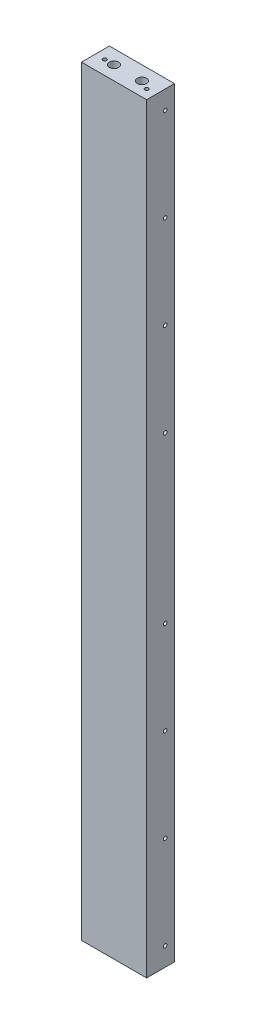
SolidWorks part; units mm, degrees
ref_plane "Front Plane" through (0, 0, 0) normal (0, 0, 1) x (1, 0, 0)
ref_plane "Top Plane" through (0, 0, 0) normal (0, 1, 0) x (1, 0, 0)
ref_plane "Right Plane" through (0, 0, 0) normal (1, 0, 0) x (0, 0, -1)
sketch "Sketch1" plane through (0, 0, 0) normal (0, 1, 0) x (1, 0, 0)
  line L1 (0, 0) -> (88.9, 0)
  line L2 (0, 0) -> (0, -38.1)
  line L3 (0, -38.1) -> (88.9, -38.1)
  line L4 (88.9, 0) -> (88.9, -38.1)
  dimension "D1" = 38.1
  dimension "D2" = 88.9
extrude "Boss-Extrude1" add sketch "Sketch1" along normal blind 1038.225
sketch "Sketch2" plane through (0, 1038.225, 0) normal (0, 1, 0) x (1, 0, 0)
  line L0 (0, 0) -> (0, -38.1) construction
  line L1 (25.4, -19.05) -> (63.5, -19.05) construction
  line L2 (88.9, 0) -> (0, 0) construction
  circle A0 centre (25.4, -19.05) radius 6.35
  circle A1 centre (63.5, -19.05) radius 6.35
  point P7 (0, -19.05)
  point P9 (44.45, 0)
  point P10 (44.45, -19.05)
  dimension "D1" = 12.7
  dimension "D2" = 12.7
  dimension "D3" = 38.1
extrude "Cut-Extrude1" cut sketch "Sketch2" against normal blind 19.05
sketch "Sketch3" plane through (0, 0, 0) normal (0, -1, 0) x (1, 0, 0)
  line L0 (25.4, 19.05) -> (63.5, 19.05) construction
  line L1 (0, 38.1) -> (88.9, 38.1) construction
  line L2 (0, 0) -> (0, 38.1) construction
  circle A0 centre (25.4, 19.05) radius 6.35
  circle A1 centre (63.5, 19.05) radius 6.35
  point P6 (44.45, 38.1)
  point P7 (44.45, 19.05)
  point P10 (0, 19.05)
  dimension "D1" = 12.7
  dimension "D2" = 12.7
  dimension "D3" = 38.1
extrude "Cut-Extrude2" cut sketch "Sketch3" against normal blind 19.05
sketch "Sketch4" plane through (0, 1038.225, 0) normal (0, 1, 0) x (1, 0, 0)
  line L0 (88.9, -38.1) -> (88.9, 0) construction
  line L1 (88.9, 0) -> (0, 0) construction
  point P0 (12.7, -19.05)
  point P1 (76.2, -25.4)
  dimension "D1" = 76.2
  dimension "D2" = 12.7
  dimension "D3" = 25.4
  dimension "D4" = 19.05
sketch "Sketch5" plane through (0, 0, 0) normal (0, -1, 0) x (1, 0, 0)
  line L0 (0, 0) -> (0, 38.1) construction
  line L1 (88.9, 0) -> (0, 0) construction
  point P0 (44.45, 25.4)
  dimension "D1" = 44.45
  dimension "D2" = 25.4
hole_wizard "#10 (0.1935) Diameter Hole1" positions "3DSketch1" profile "Sketch6" hole size "#10" standard "ANSI Inch"
sketch3d "3DSketch1"
  point P0 (44.45, 0, 25.4)
  point P3 (12.7, 1038.225, 19.05)
  point P6 (76.2, 1038.225, 25.4)
sketch "Sketch6" plane through (44.45, 0, 25.4) normal (1, 0, 0) x (0, 0, -1)
  line L0 (0, 0) -> (0, 77.6766)
  line L1 (0, 77.6766) -> (2.4574, 76.2)
  line L2 (2.4574, 76.2) -> (2.4574, 0)
  line L5 (2.4574, 0) -> (0, 0)
  line L10 (0, 77.6766) -> (-2.4575, 76.2) construction
  line L11 (0, -6.35) -> (0, 107.95) construction
  dimension "Hole Dia." = 4.9149
  dimension "Hole Depth" = 76.2
  dimension "Drill Angle" = 118
sketch "Sketch8" plane through (88.9, 0, 0) normal (1, 0, 0) x (0, 0, -1)
  line L0 (-12.7, 1038.225) -> (-12.7, 0) construction
  line L2 (-38.1, 1038.225) -> (0, 1038.225) construction
  line L3 (-38.1, 0) -> (0, 0) construction
  line L6 (0, 519.1125) -> (-38.1, 519.1125) construction
  line L7 (0, 1038.225) -> (0, 0) construction
  line L8 (-38.1, 1038.225) -> (-38.1, 0) construction
  point P3 (-12.7, 1012.825)
  point P4 (-12.7, 885.825)
  point P5 (-12.7, 25.4)
  point P6 (-12.7, 152.4)
  point P7 (-12.7, 279.4)
  point P8 (-12.7, 406.4)
  point P9 (-12.7, 758.825)
  point P10 (-12.7, 631.825)
  dimension "D1" = 25.4
  dimension "D2" = 127
  dimension "D3" = 127
  dimension "D4" = 127
  dimension "D5" = 12.7
  dimension "D6" = 12.7
hole_wizard "#10 (0.1935) Diameter Hole2" positions "3DSketch3" profile "Sketch12" hole size "#10" standard "ANSI Inch"
sketch3d "3DSketch3"
  point P0 (88.9, 25.4, 12.7)
  point P3 (88.9, 152.4, 12.7)
  point P6 (88.9, 279.4, 12.7)
  point P9 (88.9, 406.4, 12.7)
  point P12 (88.9, 631.825, 12.7)
  point P15 (88.9, 758.825, 12.7)
  point P18 (88.9, 885.825, 12.7)
  point P21 (88.9, 1012.825, 12.7)
sketch "Sketch12" plane through (88.9, 25.4, 12.7) normal (0, 1, 0) x (0, 0, -1)
  line L0 (0, 0) -> (0, 52.2766)
  line L1 (0, 52.2766) -> (2.4574, 50.8)
  line L2 (2.4574, 50.8) -> (2.4574, 0)
  line L5 (2.4574, 0) -> (0, 0)
  line L10 (0, 52.2766) -> (-2.4575, 50.8) construction
  line L11 (0, -6.35) -> (0, 107.95) construction
  dimension "Hole Dia." = 4.9149
  dimension "Hole Depth" = 50.8
  dimension "Drill Angle" = 118
